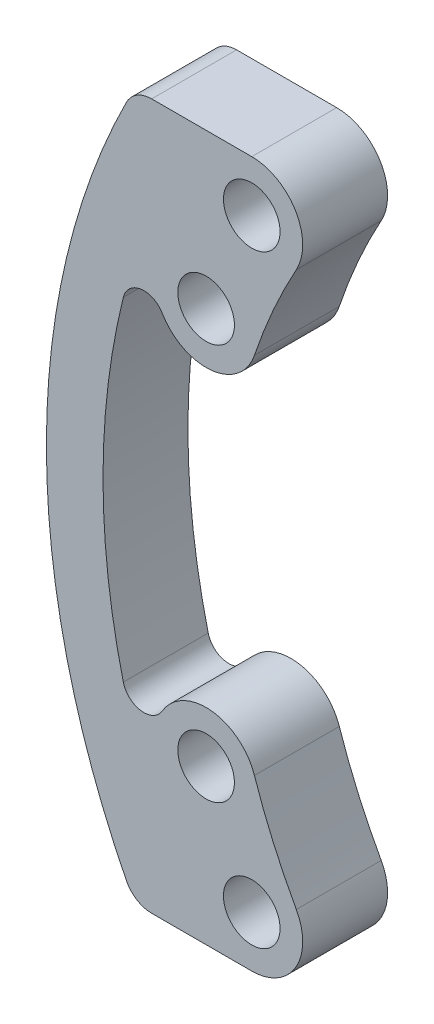
SolidWorks part; units mm, degrees
ref_plane "前视基准面" through (0, 0, 0) normal (0, 0, 1) x (1, 0, 0)
ref_plane "上视基准面" through (0, 0, 0) normal (0, 1, 0) x (1, 0, 0)
ref_plane "右视基准面" through (0, 0, 0) normal (1, 0, 0) x (0, 0, -1)
sketch "草图1" plane through (0, 0, 0) normal (0, 0, 1) x (1, 0, 0)
  line L0 (0, 0) -> (-20.8567, 0) construction
  arc A1 (-19.2445, 10.6607) -> (-20.8567, 7) centre (0, 0) ccw construction
  arc A2 (-20.819, 11.533) -> (-22.5631, 7.5727) centre (0, 0) ccw
  arc A3 (-17.6699, 9.7885) -> (-19.1502, 6.4273) centre (0, 0) ccw
  arc A4 (-17.6699, 9.7885) -> (-20.819, 11.533) centre (-19.2445, 10.6607) ccw
  arc A5 (-22.5631, 7.5727) -> (-19.1502, 6.4273) centre (-20.8567, 7) ccw
  circle A6 centre (-19.2445, 10.6607) radius 2 construction
  circle A7 centre (-20.8567, 7) radius 2 construction
  circle A8 centre (-19.2445, 10.6607) radius 1
  circle A9 centre (-20.8567, 7) radius 1
  circle A10 centre (-19.2445, -10.6607) radius 1
  circle A11 centre (-20.8567, -7) radius 1
  arc A12 (-19.2445, -10.6607) -> (-20.8567, -7) centre (0, 0) cw construction
  arc A13 (-20.819, -11.533) -> (-22.5631, -7.5727) centre (0, 0) cw
  arc A14 (-17.6699, -9.7885) -> (-19.1502, -6.4273) centre (0, 0) cw
  arc A15 (-17.6699, -9.7885) -> (-20.819, -11.533) centre (-19.2445, -10.6607) cw
  arc A16 (-22.5631, -7.5727) -> (-19.1502, -6.4273) centre (-20.8567, -7) cw
  point P5 (-20.1339, 8.8671)
  point P16 (0, 0)
  point P23 (-20.1339, -8.8671)
  dimension "D1" = 22
  dimension "D2" = 4
  dimension "D3" = 1.8
  dimension "D4" = 2
  dimension "D5" = 7
extrude "凸台-拉伸1" add sketch "草图1" along normal mid plane 3
sketch "草图2" plane through (0, 0, 1.5) normal (0, 0, 1) x (1, 0, 0)
  line L0 (-19.2445, 12.4607) -> (-23.3876, 12.4607)
  line L1 (-19.2445, -12.4607) -> (-23.3876, -12.4607)
  arc A2 (-23.7823, -5.8867) -> (-22.4079, -6.087) centre (-23.0542, -5.7065) ccw
  arc A3 (-22.4079, 6.087) -> (-23.7823, 5.8867) centre (-23.0542, 5.7065) ccw
  arc A4 (-22.5631, 7.5727) -> (-19.1502, 6.4273) centre (-20.8567, 7) ccw construction
  arc A5 (-19.1502, -6.4273) -> (-22.5631, -7.5727) centre (-20.8567, -7) ccw construction
  arc A6 (-22.4079, -6.087) -> (-22.5631, -7.5727) centre (-20.8567, -7) ccw
  arc A7 (-22.5631, 7.5727) -> (-22.4079, 6.087) centre (-20.8567, 7) ccw
  arc A8 (-23.3876, 12.4607) -> (-23.3876, -12.4607) centre (0, 0) ccw
  arc A10 (-17.6699, 9.7885) -> (-20.819, 11.533) centre (-19.2445, 10.6607) ccw construction
  arc A11 (-20.819, -11.533) -> (-17.6699, -9.7885) centre (-19.2445, -10.6607) ccw construction
  arc A12 (-22.5631, -7.5727) -> (-20.819, -11.533) centre (0, 0) ccw construction
  arc A13 (-20.819, 11.533) -> (-22.5631, 7.5727) centre (0, 0) ccw construction
  arc A14 (-20.819, -11.533) -> (-19.2445, -12.4607) centre (-19.2445, -10.6607) ccw
  arc A15 (-22.5631, -7.5727) -> (-20.819, -11.533) centre (0, 0) ccw
  arc A16 (-20.819, 11.533) -> (-22.5631, 7.5727) centre (0, 0) ccw
  arc A17 (-19.2445, 12.4607) -> (-20.819, 11.533) centre (-19.2445, 10.6607) ccw
  arc A18 (-23.7823, 5.8867) -> (-23.7823, -5.8867) centre (0, 0) ccw
  dimension "D1" = 24.5
  dimension "D2" = 1.5
  dimension "D3" = 2
extrude "凸台-拉伸2" add sketch "草图2" against normal blind 3
fillet "圆角1" radius 1 2 edges at (-23.3876, -12.4607, 0) (-23.3876, 12.4607, 0)
